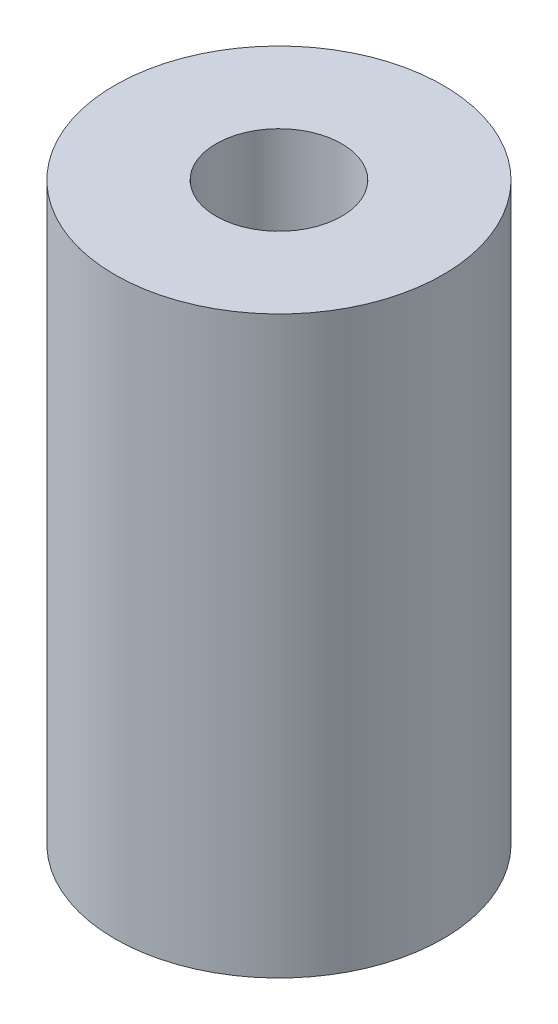
SolidWorks part; units mm, degrees
ref_plane "Front Plane" through (0, 0, 0) normal (0, 0, 1) x (1, 0, 0)
ref_plane "Top Plane" through (0, 0, 0) normal (0, 1, 0) x (1, 0, 0)
ref_plane "Right Plane" through (0, 0, 0) normal (1, 0, 0) x (0, 0, -1)
sketch "Sketch1" plane through (0, 0, 0) normal (0, 1, 0) x (1, 0, 0)
  circle A0 centre (0, 0) radius 23.5
extrude "Boss-Extrude1" add sketch "Sketch1" along normal blind 82.35
sketch "Sketch2" plane through (0, 82.35, 0) normal (0, 1, 0) x (1, 0, 0)
  circle A0 centre (0, 0) radius 9
extrude "Cut-Extrude1" cut sketch "Sketch2" against normal blind 100
